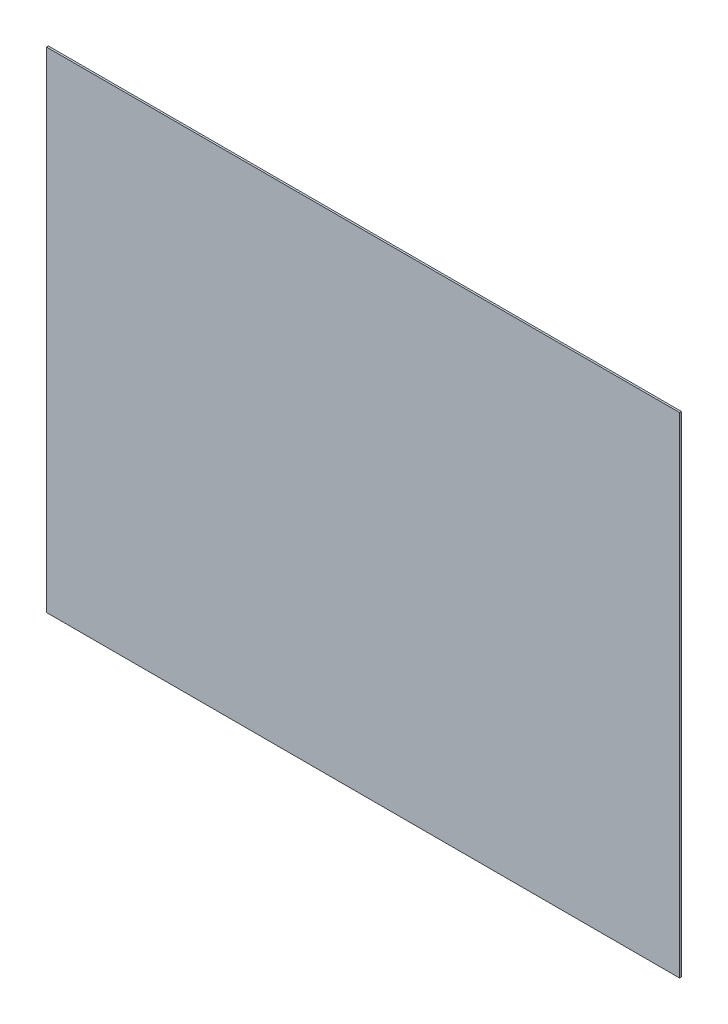
SolidWorks part; units mm, degrees
ref_plane "Front Plane" through (0, 0, 0) normal (0, 0, 1) x (1, 0, 0)
ref_plane "Top Plane" through (0, 0, 0) normal (0, 1, 0) x (1, 0, 0)
ref_plane "Right Plane" through (0, 0, 0) normal (1, 0, 0) x (0, 0, -1)
sketch "Sketch1" plane through (0, 0, 0) normal (0, 0, 1) x (1, 0, 0)
  line L1 (-533.4, 412.75) -> (533.4, 412.75)
  line L2 (-533.4, 412.75) -> (-533.4, -412.75)
  line L3 (-533.4, -412.75) -> (533.4, -412.75)
  line L4 (533.4, 412.75) -> (533.4, -412.75)
  line L5 (-533.4, 412.75) -> (533.4, -412.75) construction
  line L6 (-533.4, -412.75) -> (533.4, 412.75) construction
  point P0 (0, 0)
  dimension "D1" = 1066.8
  dimension "D2" = 825.5
extrude "Boss-Extrude1" add sketch "Sketch1" along normal blind 3.175
